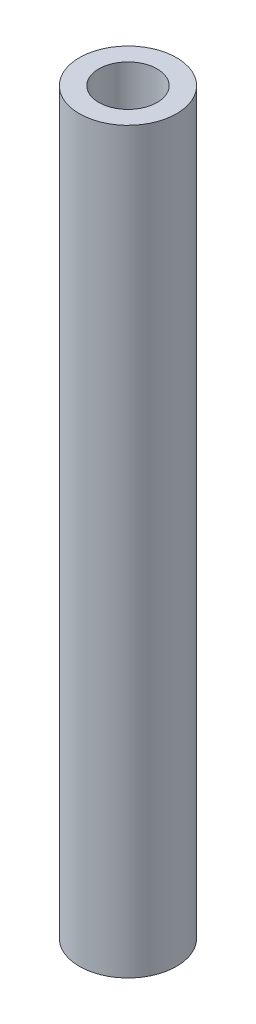
SolidWorks part; units mm, degrees
ref_plane "前视基准面" through (0, 0, 0) normal (0, 0, 1) x (1, 0, 0)
ref_plane "上视基准面" through (0, 0, 0) normal (0, 1, 0) x (1, 0, 0)
ref_plane "右视基准面" through (0, 0, 0) normal (1, 0, 0) x (0, 0, -1)
sketch "草图1" plane through (0, 0, 0) normal (0, 1, 0) x (1, 0, 0)
  circle A0 centre (0, 0) radius 2.5
  circle A1 centre (0, 0) radius 1.5
  dimension "D1" = 3
  dimension "D2" = 5
extrude "凸台-拉伸1" add sketch "草图1" along normal mid plane 38
